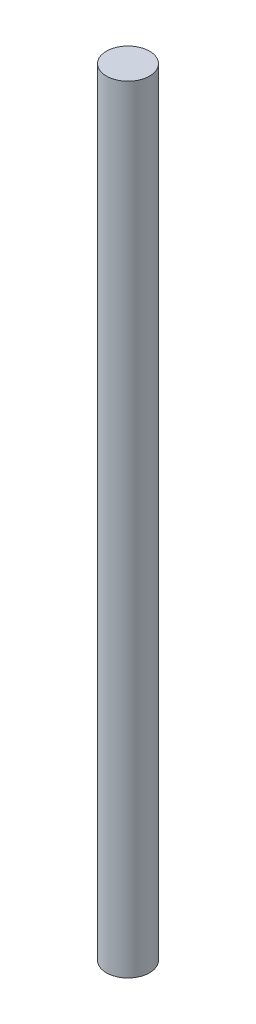
SolidWorks part; units mm, degrees
material "6061-T6 (SS)"
ref_plane "Front Plane" through (0, 0, 0) normal (0, 0, 1) x (1, 0, 0)
ref_plane "Top Plane" through (0, 0, 0) normal (0, 1, 0) x (1, 0, 0)
ref_plane "Right Plane" through (0, 0, 0) normal (1, 0, 0) x (0, 0, -1)
sketch "Sketch1" plane through (0, 0, 0) normal (0, 1, 0) x (1, 0, 0)
  circle A0 centre (0, 0) radius 6.35
  dimension "D1" = 12.7
extrude "Boss-Extrude1" add sketch "Sketch1" along normal blind 228.6
